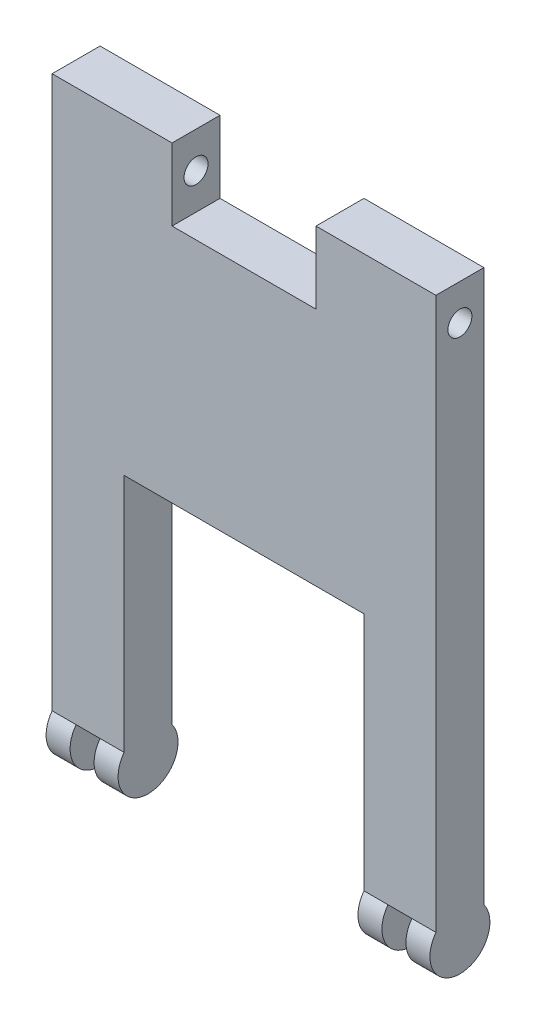
SolidWorks part; units mm, degrees
material "Nylon 101"
ref_plane "Front Plane" through (0, 0, 0) normal (0, 0, 1) x (1, 0, 0)
ref_plane "Top Plane" through (0, 0, 0) normal (0, 1, 0) x (1, 0, 0)
ref_plane "Right Plane" through (0, 0, 0) normal (1, 0, 0) x (0, 0, -1)
sketch "Sketch1" plane through (0, 0, 0) normal (0, 0, 1) x (1, 0, 0)
  line L0 (50, -115) -> (80, -115)
  line L1 (-80, -115) -> (-50, -115)
  line L2 (-80, -115) -> (-80, 115)
  line L3 (-80, 115) -> (80, 115)
  line L4 (80, -115) -> (80, 115)
  line L5 (-80, -115) -> (80, 115) construction
  line L6 (-80, 115) -> (80, -115) construction
  line L8 (-50, -115) -> (-50, -15)
  line L9 (-50, -15) -> (50, -15)
  line L10 (50, -115) -> (50, -15)
  line L11 (-50, -115) -> (50, -15) construction
  line L12 (-50, -15) -> (50, -115) construction
  point P0 (0, 0)
  point P6 (0, -65)
  dimension "D1" = 160
  dimension "D2" = 230
  dimension "D3" = 100
  dimension "D4" = 100
extrude "Boss-Extrude2" add sketch "Sketch1" against normal blind 20
sketch "Sketch2" plane through (0, 0, 0) normal (1, 0, 0) x (0, 0, -1)
  circle A0 centre (10, -122.5) radius 12.5
  dimension "D1" = 25
extrude "Cut-Extrude1" cut sketch "Sketch2" along normal mid plane 160
sketch "Sketch3" plane through (80, 0, 0) normal (1, 0, 0) x (0, 0, -1)
  circle A0 centre (10, -122.5) radius 12.5
  arc A1 (20, -115) -> (0, -115) centre (10, -122.5) ccw construction
  dimension "D1" = 25
extrude "Boss-Extrude3" add sketch "Sketch3" against normal blind 10
mirror "Mirror1" about plane through (0, 0, 0) normal (1, 0, 0) of "Boss-Extrude3"
sketch "Sketch4" plane through (50, 0, 0) normal (-1, 0, 0) x (0, 0, 1)
  circle A0 centre (-10, -122.5) radius 12.5
  arc A1 (0, -115) -> (-20, -115) centre (-10, -122.5) ccw construction
  dimension "D1" = 25
extrude "Boss-Extrude4" add sketch "Sketch4" against normal blind 10
mirror "Mirror2" about plane through (0, 0, 0) normal (1, 0, 0) of "Boss-Extrude4"
sketch "Sketch5" plane through (80, 0, 0) normal (1, 0, 0) x (0, 0, -1)
  line L0 (20, -115) -> (20, 115) construction
  line L1 (20, 115) -> (0, 115) construction
  circle A0 centre (10, 100) radius 5
  dimension "D1" = 10
  dimension "D2" = 10
  dimension "D3" = 15
extrude "Cut-Extrude2" cut sketch "Sketch5" against normal up to next
sketch "Sketch6" plane through (0, 115, 0) normal (0, 1, 0) x (1, 0, 0)
  line L0 (80, 20) -> (-80, 20) construction
  line L1 (-30, 0) -> (30, 0)
  line L2 (-30, 0) -> (-30, 20)
  line L3 (-30, 20) -> (30, 20)
  line L4 (30, 0) -> (30, 20)
  line L5 (-30, 0) -> (30, 20) construction
  line L6 (-30, 20) -> (30, 0) construction
  point P0 (0, 10)
  dimension "D1" = 60
extrude "Cut-Extrude3" cut sketch "Sketch6" against normal blind 30
